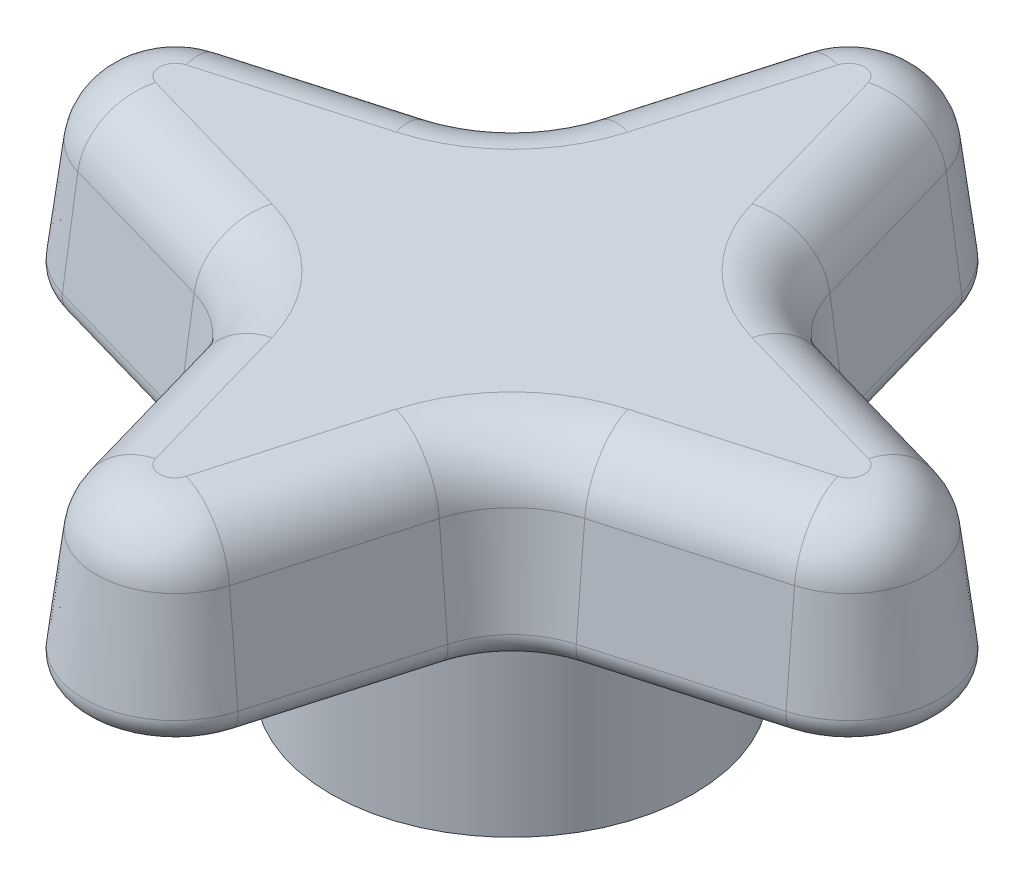
SolidWorks part; units mm, degrees
ref_plane "Front" through (0, 0, 0) normal (0, 0, 1) x (1, 0, 0)
ref_plane "Top" through (0, 0, 0) normal (0, 1, 0) x (1, 0, 0)
ref_plane "Right" through (0, 0, 0) normal (1, 0, 0) x (0, 0, -1)
sketch "Sketch1" plane through (0, 0, 0) normal (0, 1, 0) x (1, 0, 0)
  line L0 (0, 27.0019) -> (0, -27.0019) construction
  line L1 (-27.0019, 0) -> (27.0019, 0) construction
  line L2 (3.175, 12.7) -> (4.8125, 6.9894)
  line L3 (12.7, 3.175) -> (6.9894, 4.8125)
  line L4 (0, 0) -> (48.4155, 48.4155) construction
  line L5 (-12.7, 3.175) -> (-6.9894, 4.8125)
  line L6 (-3.175, 12.7) -> (-4.8125, 6.9894)
  line L7 (-3.175, -12.7) -> (-4.8125, -6.9894)
  line L8 (-12.7, -3.175) -> (-6.9894, -4.8125)
  line L9 (12.7, -3.175) -> (6.9894, -4.8125)
  line L10 (3.175, -12.7) -> (4.8125, -6.9894)
  arc A0 (4.8125, 6.9894) -> (6.9894, 4.8125) centre (7.8645, 7.8645) ccw
  arc A1 (-4.8125, 6.9894) -> (-6.9894, 4.8125) centre (-7.8645, 7.8645) cw
  arc A2 (-4.8125, -6.9894) -> (-6.9894, -4.8125) centre (-7.8645, -7.8645) ccw
  arc A3 (4.8125, -6.9894) -> (6.9894, -4.8125) centre (7.8645, -7.8645) cw
  arc A4 (12.7, 3.175) -> (12.7, -3.175) centre (11.7896, 0) cw
  arc A5 (3.175, -12.7) -> (-3.175, -12.7) centre (0, -11.7896) cw
  arc A6 (-12.7, -3.175) -> (-12.7, 3.175) centre (-11.7896, 0) cw
  arc A7 (-3.175, 12.7) -> (3.175, 12.7) centre (0, 11.7896) cw
  dimension "D4" = 3.175
  dimension "D1" = 16
  dimension "D2" = 6.35
  dimension "D3" = 45
  dimension "D5" = 12.7
extrude "Extrude1" add sketch "Sketch1" along normal blind 6.35 draft 7
fillet "Fillet1" radius 2.2225
sketch "Sketch2" plane through (0, 0, 0) normal (0, -1, 0) x (1, 0, 0)
  circle A0 centre (0, 0) radius 6.35
  circle A1 centre (0, 0) radius 4.7625
  dimension "D1" = 12.7
  dimension "D2" = 9.525
extrude "Extrude2" add sketch "Sketch2" along normal blind 6.35
fillet "Fillet2" radius 0.762
